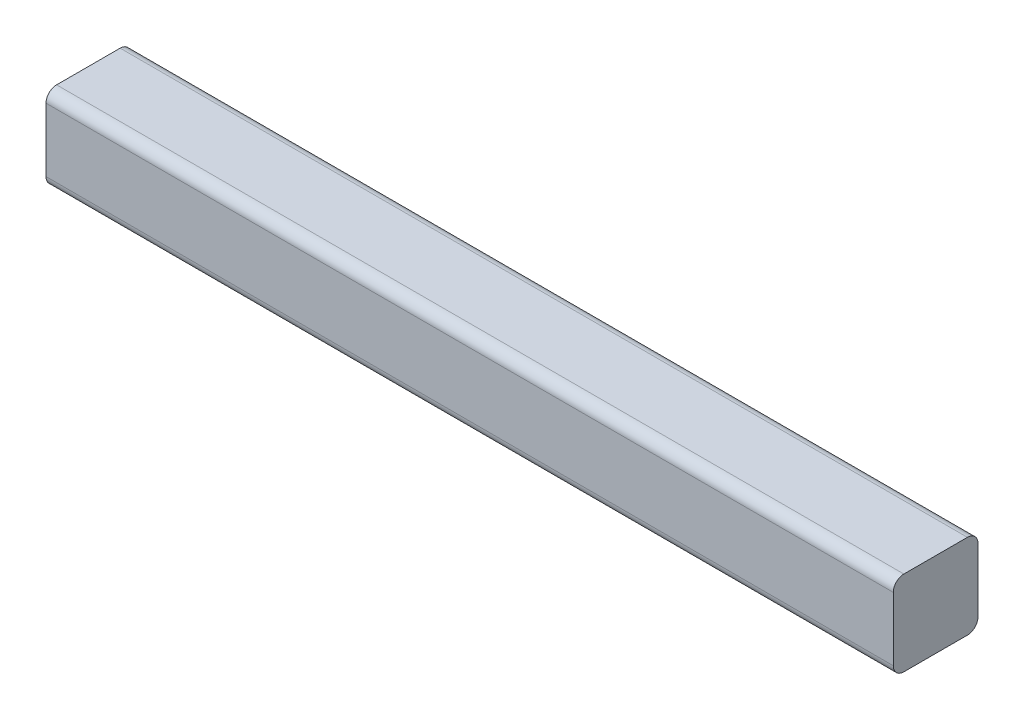
SolidWorks part; units mm, degrees
ref_plane "Front Plane" through (0, 0, 0) normal (0, 0, 1) x (1, 0, 0)
ref_plane "Top Plane" through (0, 0, 0) normal (0, 1, 0) x (1, 0, 0)
ref_plane "Right Plane" through (0, 0, 0) normal (1, 0, 0) x (0, 0, -1)
sketch "Sketch1" plane through (0, 0, 0) normal (1, 0, 0) x (0, 0, -1)
  line L1 (0, 0) -> (-12.7, 0)
  line L2 (0, 0) -> (0, -12.7)
  line L3 (0, -12.7) -> (-12.7, -12.7)
  line L4 (-12.7, 0) -> (-12.7, -12.7)
  dimension "D1" = 12.7
  dimension "D2" = 12.7
extrude "Boss-Extrude1" add sketch "Sketch1" along normal blind 127
fillet "Fillet1" radius 1.5875 4 edges at (63.5, -12.7, 0) (63.5, -12.7, 12.7) (63.5, 0, 0) (63.5, 0, 12.7)
